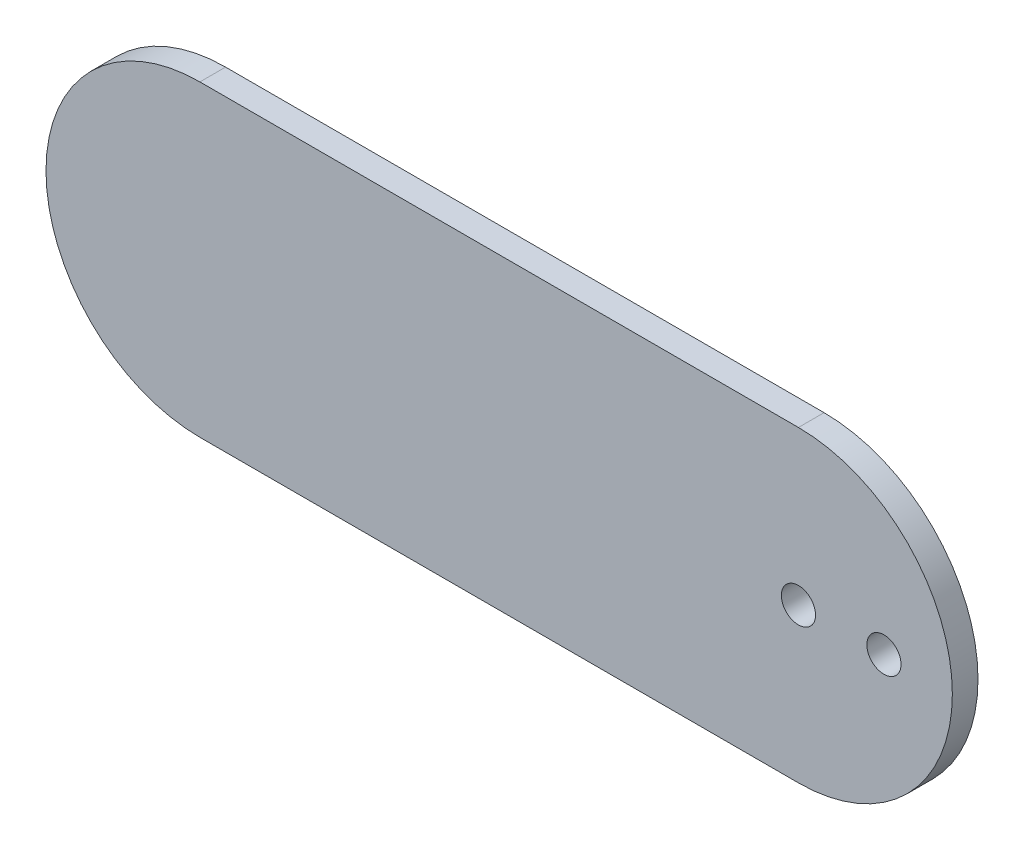
SolidWorks part; units mm, degrees
ref_plane "Front Plane" through (0, 0, 0) normal (0, 0, 1) x (1, 0, 0)
ref_plane "Top Plane" through (0, 0, 0) normal (0, 1, 0) x (1, 0, 0)
ref_plane "Right Plane" through (0, 0, 0) normal (1, 0, 0) x (0, 0, -1)
sketch "Sketch1" plane through (0, 0, 0) normal (0, 0, 1) x (1, 0, 0)
  line L1 (0, 18) -> (-70, 18)
  line L2 (0, -18) -> (-70, -18)
  arc A0 (0, -18) -> (0, 18) centre (0, 0) ccw
  arc A1 (-70, 18) -> (-70, -18) centre (-70, 0) ccw
  circle A2 centre (0, 0) radius 2
  dimension "D1" = 4
  dimension "D2" = 18
  dimension "D3" = 18
  dimension "D4" = 70
  dimension "D5" = 70
  dimension "D6" = 36
extrude "Boss-Extrude1" add sketch "Sketch1" along normal blind 3
sketch "Sketch2" plane through (0, 0, 3) normal (0, 0, 1) x (1, 0, 0)
  text T0 "ARM" font "Century Gothic" height in points 22
  dimension "D1" = 9.5
  dimension "D2" = 5
sketch "Sketch3" plane through (0, 0, 3) normal (0, 0, 1) x (1, 0, 0)
  circle A0 centre (10, 0) radius 2
  dimension "D1" = 10
  dimension "D2" = 4
  dimension "D3" = 5
extrude "Cut-Extrude1" cut sketch "Sketch3" against normal blind 3
